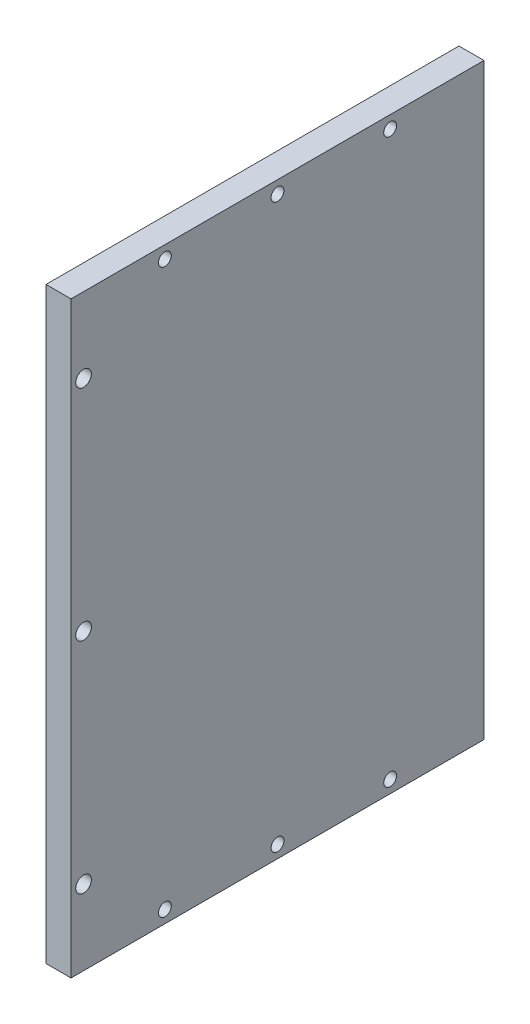
SolidWorks part; units mm, degrees
ref_plane "前视基准面" through (0, 0, 0) normal (0, 0, 1) x (1, 0, 0)
ref_plane "上视基准面" through (0, 0, 0) normal (0, 1, 0) x (1, 0, 0)
ref_plane "右视基准面" through (0, 0, 0) normal (1, 0, 0) x (0, 0, -1)
sketch "草图1" plane through (0, 0, 0) normal (1, 0, 0) x (0, 0, -1)
  line L0 (0, 0) -> (0, 47)
  line L1 (0, 0) -> (0, -47)
  line L2 (66, 47) -> (66, -47)
  line L3 (0, 47) -> (66, 47)
  line L4 (66, -47) -> (0, -47)
  circle A0 centre (2, 0) radius 1.25
  circle A1 centre (2, 35) radius 1.25
  circle A2 centre (2, -35) radius 1.25
  dimension "D1" = 2
  dimension "D2" = 2
extrude "凸台-拉伸1" add sketch "草图1" along normal blind 4
sketch "草图2" plane through (0, 0, 0) normal (1, 0, 0) x (0, 0, -1)
  line L0 (66, -45) -> (51, -45)
  line L1 (0, -45) -> (15, -45)
  line L4 (0, 45) -> (15, 45)
  line L5 (66, 45) -> (51, 45)
  line L7 (0, 0) -> (66, 0) construction
hole_wizard "M2.5 螺纹孔1" positions "草图3" profile "草图4" tap size "M2.5" standard "GB" end condition through all
sketch "草图3" plane through (4, 0, 0) normal (1, 0, 0) x (0, 0, -1)
  point P0 (15, 45)
  point P3 (51, 45)
  point P6 (15, -45)
  point P9 (51, -45)
  point P12 (33, -45)
  point P14 (33, 45)
sketch "草图4" plane through (4, 45, -15) normal (0, 1, 0) x (0, 0, -1)
  line L0 (0, 0) -> (0, 4)
  line L1 (0, 4) -> (1.025, 4)
  line L2 (1.025, 4) -> (1.025, 0)
  line L5 (1.025, 0) -> (0, 0)
  line L11 (0, -6.35) -> (0, 107.95) construction
  dimension "通孔螺纹孔钻头直径" = 2.05
  dimension "通孔螺纹孔钻头深度" = 4
cosmetic thread "孔螺蚊线1" parameters "D2"=2.5
cosmetic thread "孔螺蚊线2" parameters "D2"=2.5
cosmetic thread "孔螺蚊线3" parameters "D2"=2.5
cosmetic thread "孔螺蚊线4" parameters "D2"=2.5
cosmetic thread "孔螺蚊线5" parameters "D2"=2.5
cosmetic thread "孔螺蚊线6" parameters "D2"=2.5
ref_plane "基准面1" through (0, 0, -66) normal (0, 0, -1) x (-1, 0, 0)
sketch "草图5" plane through (0, 0, -66) normal (0, 0, -1) x (-1, 0, 0)
  circle A0 centre (-2, 0) radius 1.25
  circle A1 centre (-2, 35) radius 1.25
  circle A2 centre (-2, -35) radius 1.25
  dimension "D1" = 2
  dimension "D2" = 2
hole_wizard "M2.5 螺纹孔2" positions "草图6" profile "草图7" tap size "M2.5" standard "GB"
sketch "草图6" plane through (0, 0, -66) normal (0, 0, -1) x (-1, 0, 0)
  point P0 (-2, 35)
  point P3 (-2, 0)
  point P6 (-2, -35)
sketch "草图7" plane through (2, 35, -66) normal (1, 0, 0) x (0, 1, 0)
  line L0 (0, 0) -> (0, 7.8659)
  line L1 (0, 7.8659) -> (1.025, 7.25)
  line L2 (1.025, 7.25) -> (1.025, 0)
  line L5 (1.025, 0) -> (0, 0)
  line L10 (0, 7.8659) -> (-1.025, 7.25) construction
  line L11 (0, -6.35) -> (0, 107.95) construction
  dimension "螺纹孔钻头直径" = 2.05
  dimension "螺纹孔钻头深度" = 7.25
  dimension "导头角度" = 118
cosmetic thread "孔螺蚊线7" parameters "D1"=5, "D2"=2.5
cosmetic thread "孔螺蚊线8" parameters "D1"=5, "D2"=2.5
cosmetic thread "孔螺蚊线9" parameters "D1"=5, "D2"=2.5
